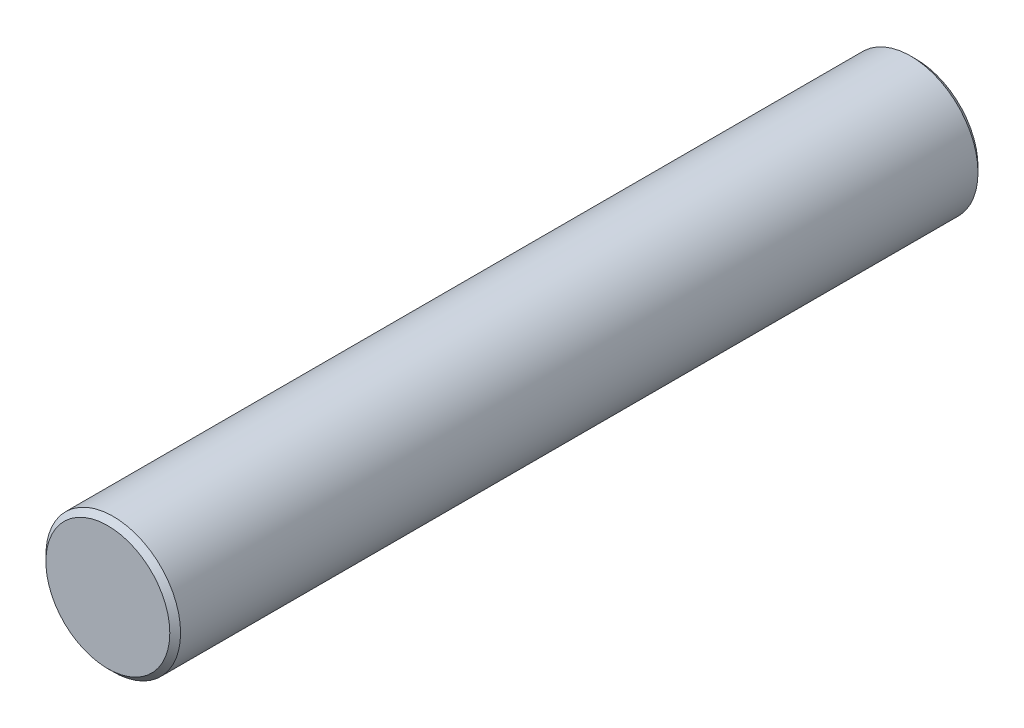
SolidWorks part; units mm, degrees
ref_plane "Front Plane" through (0, 0, 0) normal (0, 0, 1) x (1, 0, 0)
ref_plane "Top Plane" through (0, 0, 0) normal (0, 1, 0) x (1, 0, 0)
ref_plane "Right Plane" through (0, 0, 0) normal (1, 0, 0) x (0, 0, -1)
sketch "Sketch2" plane through (0, 0, 0) normal (0, 0, 1) x (1, 0, 0)
  circle A0 centre (0, 0) radius 2.5
  dimension "D1" = 5
extrude "Boss-Extrude1" add sketch "Sketch2" along normal blind 30
chamfer "Chamfer1" distance 0.2 angle 45 2 edges at (2.5, 0, 30) (2.5, 0, 0)
